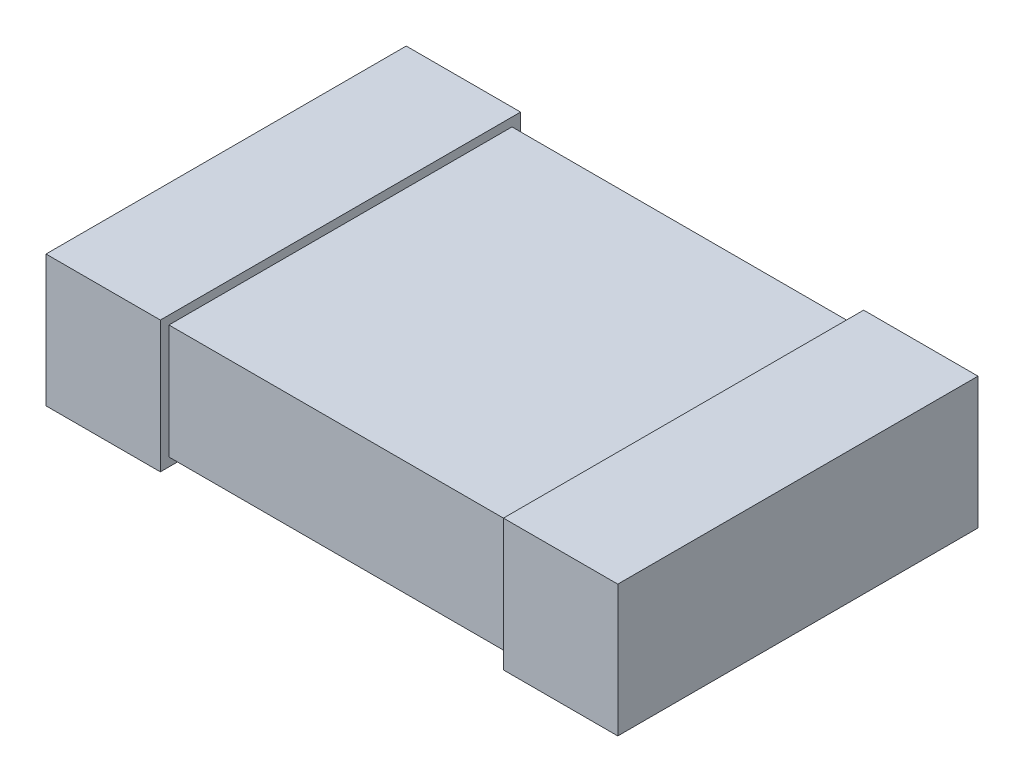
SolidWorks part; units mm, degrees
ref_plane "Front Plane" through (0, 0, 0) normal (0, 0, 1) x (1, 0, 0)
ref_plane "Top Plane" through (0, 0, 0) normal (0, 1, 0) x (1, 0, 0)
ref_plane "Right Plane" through (0, 0, 0) normal (1, 0, 0) x (0, 0, -1)
sketch "Sketch1" plane through (0, 0, 0) normal (0, 1, 0) x (1, 0, 0)
  line L1 (-1, 0.6) -> (1, 0.6)
  line L2 (-1, 0.6) -> (-1, -0.6)
  line L3 (-1, -0.6) -> (1, -0.6)
  line L4 (1, 0.6) -> (1, -0.6)
  point P4 (0, 0.6)
  point P6 (1, 0)
  dimension "D1" = 1.2
  dimension "D2" = 2
extrude "Extrude1" add sketch "Sketch1" along normal blind 0.4
sketch "Sketch2" plane through (0, 0, 0) normal (0, 0, 1) x (1, 0, 0)
  line L0 (-1, 0.4) -> (-1, 0) construction
  line L1 (-0.6, 0.43) -> (-1, 0.43)
  line L2 (-0.6, 0.43) -> (-0.6, -0.03)
  line L3 (-0.6, -0.03) -> (-1, -0.03)
  line L4 (-1, 0.43) -> (-1, -0.03)
  line L5 (-1, 0.4) -> (1, 0.4) construction
  line L6 (-1, 0) -> (1, 0) construction
  line L7 (0, 0) -> (0, -0.3575) construction
  line L8 (1, 0.43) -> (1, -0.03)
  line L9 (0.6, -0.03) -> (1, -0.03)
  line L10 (0.6, 0.43) -> (0.6, -0.03)
  line L11 (0.6, 0.43) -> (1, 0.43)
  dimension "D1" = 0.4
  dimension "D2" = 0.03
  dimension "D3" = 0.03
extrude "Extrude2" add sketch "Sketch2" along normal offset from surface 0.03 and the other way offset from surface (0.63 mm away) 0.03 up to face at (0, 0.2, 0.6) offset beyond the face yes other way up to face at (0, 0.2, -0.6)
ref_plane "Board Surface" through (0, -0.03, 0) normal (0, 1, 0) x (-1, 0, 0)
sketch "Component_Outline" plane through (0, -0.03, 0) normal (0, 1, 0) x (-1, 0, 0)
  line L0 (0.6, 0.6) -> (-0.6, 0.6)
  line L1 (-0.6, 0.6) -> (-0.6, 0.63)
  line L2 (-0.6, 0.63) -> (-1, 0.63)
  line L3 (-1, 0.63) -> (-1, -0.63)
  line L4 (-1, -0.63) -> (-0.6, -0.63)
  line L5 (-0.6, -0.63) -> (-0.6, -0.6)
  line L6 (-0.6, -0.6) -> (0.6, -0.6)
  line L7 (0.6, -0.6) -> (0.6, -0.63)
  line L8 (0.6, -0.63) -> (1, -0.63)
  line L9 (1, -0.63) -> (1, 0.63)
  line L10 (1, 0.63) -> (0.6, 0.63)
  line L11 (0.6, 0.63) -> (0.6, 0.6)
  point P24 (0, 0)
